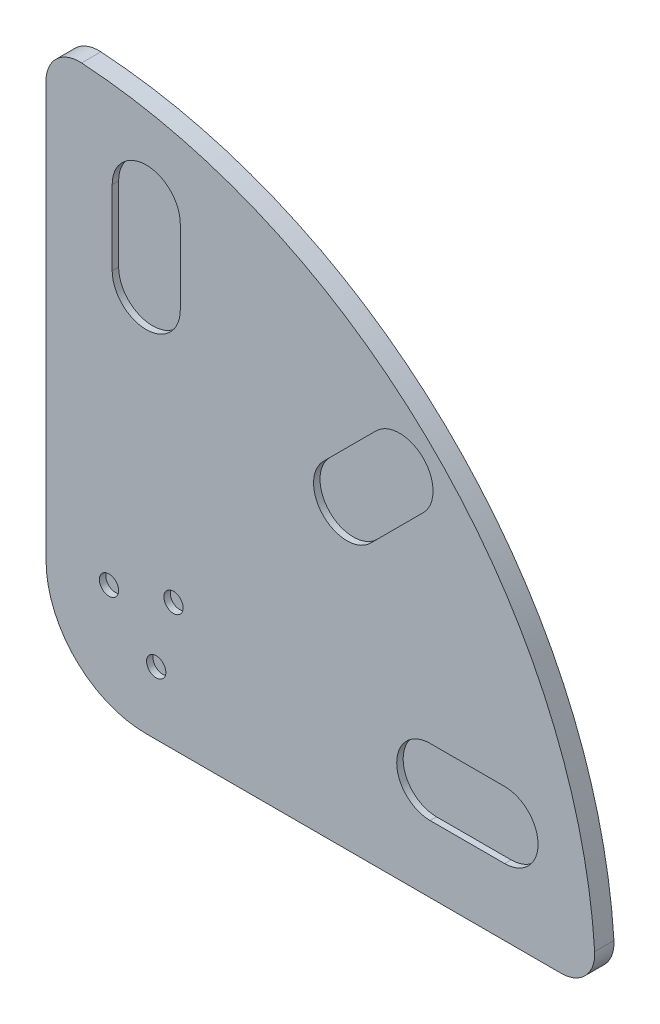
SolidWorks part; units mm, degrees
material "ABS"
ref_plane "Ön Düzlem" through (0, 0, 0) normal (0, 0, 1) x (1, 0, 0)
ref_plane "Üst Düzlem" through (0, 0, 0) normal (0, 1, 0) x (1, 0, 0)
ref_plane "Sağ Düzlem" through (0, 0, 0) normal (1, 0, 0) x (0, 0, -1)
sketch "Çizim1" plane through (0, 0, 0) normal (0, 0, 1) x (1, 0, 0)
  line L0 (-78, 0) -> (-78, 350)
  line L1 (0, -78) -> (350, -78)
  arc A0 (-78, 0) -> (0, -78) centre (0, 0) ccw
  arc A1 (-78, 350) -> (350, -78) centre (-78, -78) cw
  dimension "D1" = 156
  dimension "D2" = 350
extrude "Yükseklik-Ekstrüzyon1" add sketch "Çizim1" along normal blind 15
sketch "Çizim2" plane through (0, 0, 15) normal (0, 0, 1) x (1, 0, 0)
  line L0 (21.2132, 21.2132) -> (0, 0) construction
  line L1 (-78, 350) -> (-78, 0) construction
  line L2 (0, 279) -> (0, 221) construction
  line L3 (26.5, 279) -> (26.5, 221)
  line L4 (-26.5, 279) -> (-26.5, 221)
  line L5 (197.2828, 197.2828) -> (156.2706, 156.2706) construction
  line L6 (215.6676, 178.898) -> (174.6554, 137.8858)
  line L7 (178.898, 215.6676) -> (137.8858, 174.6554)
  line L8 (221, 0) -> (279, 0) construction
  line L9 (221, 26) -> (279, 26)
  line L10 (221, -26) -> (279, -26)
  line L11 (0, -78) -> (350, -78) construction
  circle A0 centre (21.2132, 21.2132) radius 7.5
  circle A1 centre (7.7646, -28.9778) radius 7.5
  circle A2 centre (-28.9778, 7.7646) radius 7.5
  arc A3 (26.5, 279) -> (-26.5, 279) centre (0, 279) ccw
  arc A4 (-26.5, 221) -> (26.5, 221) centre (0, 221) ccw
  arc A5 (215.6676, 178.898) -> (178.898, 215.6676) centre (197.2828, 197.2828) ccw
  arc A6 (137.8858, 174.6554) -> (174.6554, 137.8858) centre (156.2706, 156.2706) ccw
  arc A7 (221, 26) -> (221, -26) centre (221, 0) ccw
  arc A8 (279, -26) -> (279, 26) centre (279, 0) ccw
  circle A9 centre (221, 0) radius 26 construction
  circle A10 centre (279, 0) radius 26 construction
  circle A11 centre (156.2706, 156.2706) radius 26 construction
  circle A12 centre (197.2828, 197.2828) radius 26 construction
  circle A13 centre (0, 221) radius 26.5 construction
  circle A14 centre (0, 279) radius 26.5 construction
  point P10 (0, 0)
  point P11 (0, 250)
  point P18 (0, 279)
  point P19 (0, 221)
  point P20 (176.7767, 176.7767)
  point P28 (250, 0)
  point P36 (197.2828, 197.2828)
  point P37 (156.2706, 156.2706)
  point P38 (279, 0)
  point P39 (221, 0)
  dimension "D1" = 15
  dimension "D3" = 3
  dimension "D4" = 45
  dimension "D6" = 58
  dimension "D5" = 26.5
  dimension "D8" = 26
  dimension "D10" = 26
  dimension "D12" = 52
  dimension "D15" = 52
  dimension "D16" = 52
  dimension "D17" = 52
  dimension "D18" = 53
  dimension "D19" = 53
  dimension "D2" = 30
  dimension "D7" = 250
  dimension "D9" = 58
  dimension "D11" = 58
  dimension "D13" = 250
  dimension "D14" = 250
extrude "Kes-Ekstrüzyon1" cut sketch "Çizim2" against normal blind 5
fillet "Radyus1" radius 26 2 edges at (350, -78, 7.5) (-78, 350, 7.5)
sketch "referans" plane through (0, 0, 15) normal (0, 0, 1) x (1, 0, 0)
  line L0 (0, 0) -> (78, 0) construction
  line L1 (0, 0) -> (0, 78) construction
  circle A0 centre (0, 0) radius 78 construction
  point P9 (0, 0)
  dimension "D1" = 156
